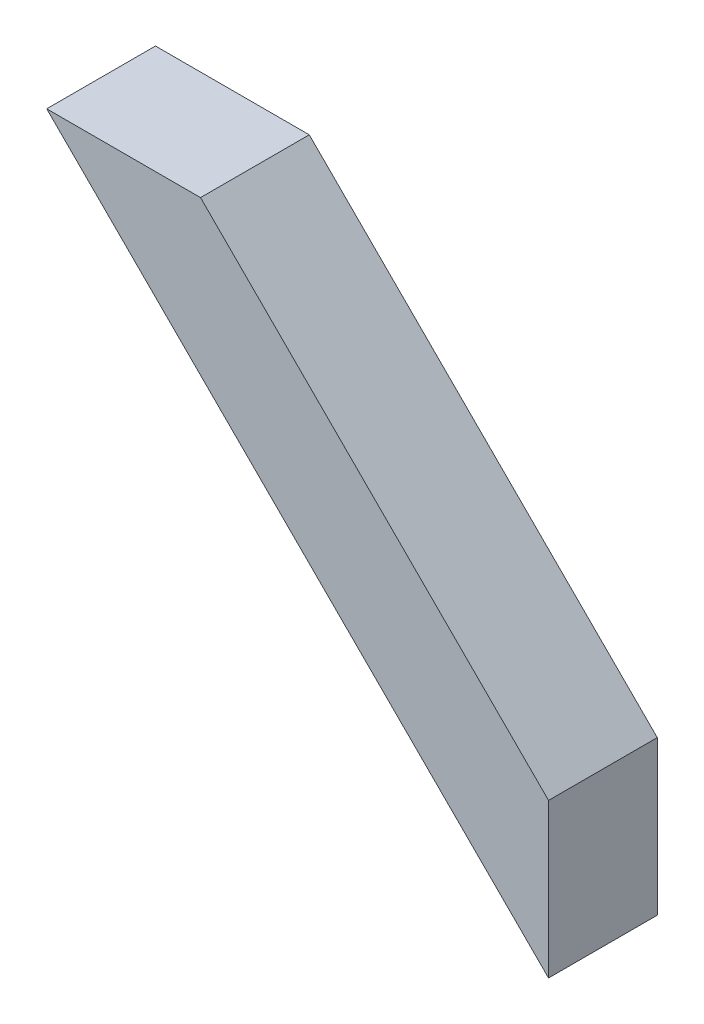
SolidWorks part; units mm, degrees
ref_plane "Alzado" through (0, 0, 0) normal (0, 0, 1) x (1, 0, 0)
ref_plane "Planta" through (0, 0, 0) normal (0, 1, 0) x (1, 0, 0)
ref_plane "Vista lateral" through (0, 0, 0) normal (1, 0, 0) x (0, 0, -1)
sketch "Croquis1" plane through (0, 0, 0) normal (0, 0, 1) x (1, 0, 0)
  line L0 (0, 0) -> (0, 203.2) construction
  line L1 (0, 203.2) -> (-203.2, 203.2) construction
  line L2 (-203.2, 203.2) -> (0, 0)
  line L3 (-293.0026, 203.2) -> (0, -89.8026)
  line L4 (-203.2, 203.2) -> (-293.0026, 203.2)
  line L5 (0, 0) -> (0, -89.8026)
  dimension "D1" = 203.2
  dimension "D2" = 203.2
  dimension "D3" = 63.5
extrude "Saliente-Extruir1" add sketch "Croquis1" along normal blind 63.5
